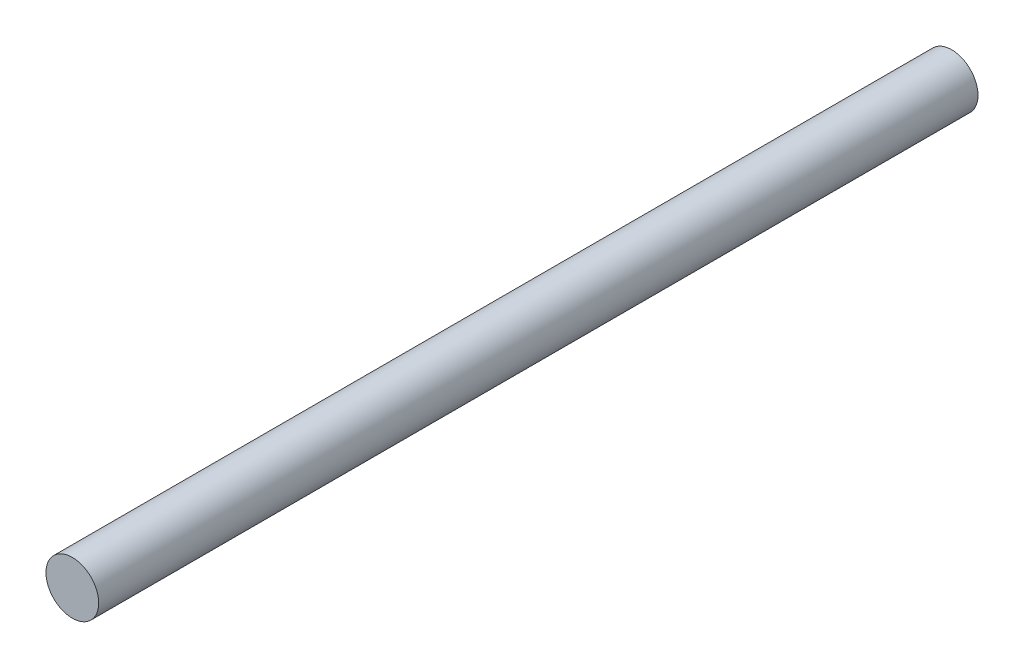
SolidWorks part; units mm, degrees
ref_plane "Front Plane" through (0, 0, 0) normal (0, 0, 1) x (1, 0, 0)
ref_plane "Top Plane" through (0, 0, 0) normal (0, 1, 0) x (1, 0, 0)
ref_plane "Right Plane" through (0, 0, 0) normal (1, 0, 0) x (0, 0, -1)
sketch "Sketch1" plane through (0, 0, 0) normal (0, 0, 1) x (1, 0, 0)
  circle A0 centre (0, 0) radius 1.5
  dimension "D1" = 3
extrude "Boss-Extrude1" add sketch "Sketch1" along normal blind 50
